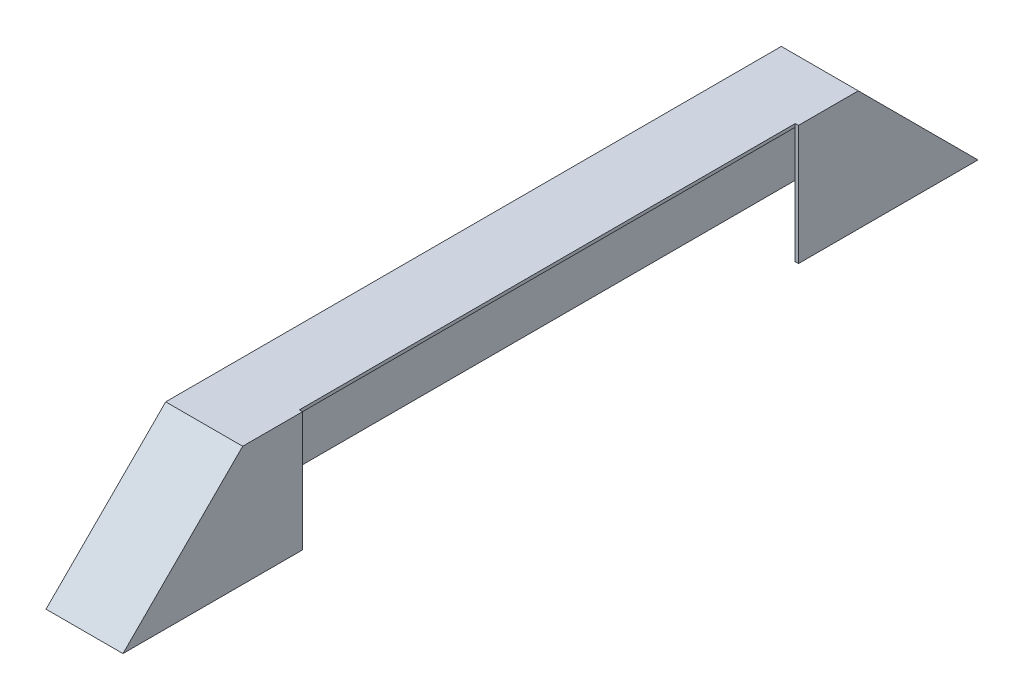
SolidWorks part; units mm, degrees
ref_plane "Front Plane" through (0, 0, 0) normal (0, 0, 1) x (1, 0, 0)
ref_plane "Top Plane" through (0, 0, 0) normal (0, 1, 0) x (1, 0, 0)
ref_plane "Right Plane" through (0, 0, 0) normal (1, 0, 0) x (0, 0, -1)
sketch "Sketch1" plane through (0, 0, 0) normal (1, 0, 0) x (0, 0, -1)
  line L0 (-457.2, 88.9) -> (-635, -88.9)
  line L1 (-457.2, -88.9) -> (457.2, -88.9)
  line L2 (457.2, 88.9) -> (457.2, -88.9) construction
  line L3 (-457.2, 88.9) -> (457.2, 88.9)
  line L4 (-457.2, 88.9) -> (-457.2, -88.9) construction
  line L5 (-457.2, -88.9) -> (457.2, 88.9) construction
  line L6 (-457.2, 88.9) -> (457.2, -88.9) construction
  line L7 (-635, -88.9) -> (-457.2, -88.9)
  line L8 (457.2, 88.9) -> (635, -88.9)
  line L9 (457.2, -88.9) -> (635, -88.9)
  point P0 (0, 0)
  dimension "D1" = 914.4
  dimension "D2" = 177.8
  dimension "D3" = 251.4472
  dimension "D4" = 1270
extrude "Boss-Extrude1" add sketch "Sketch1" along normal blind 114.3
shell "Shell3" thickness 4.7625
sketch "Sketch8" plane through (114.3, 0, 0) normal (1, 0, 0) x (0, 0, -1)
  line L0 (457.2, 88.9) -> (-457.2, 88.9) construction
  line L1 (-368.3, -88.9) -> (368.3, -88.9)
  line L2 (-368.3, -88.9) -> (-368.3, 88.9)
  line L3 (-368.3, 88.9) -> (368.3, 88.9)
  line L4 (368.3, -88.9) -> (368.3, 88.9)
  line L5 (-368.3, -88.9) -> (368.3, 88.9) construction
  line L6 (-368.3, 88.9) -> (368.3, -88.9) construction
  point P0 (0, 0)
  dimension "D1" = 177.8
  dimension "D2" = 736.6
extrude "Cut-Extrude2" cut sketch "Sketch8" against normal up to surface (4.7625 mm away) up to face at (109.5375, -2.3813, 0)
sketch "Bend-Lines3" plane through (0, 0, 0) normal (0, 1, 0) x (1, 0, 0)
sketch "Bounding-Box3" plane through (0, 0, 0) normal (0, 1, 0) x (1, 0, 0)
